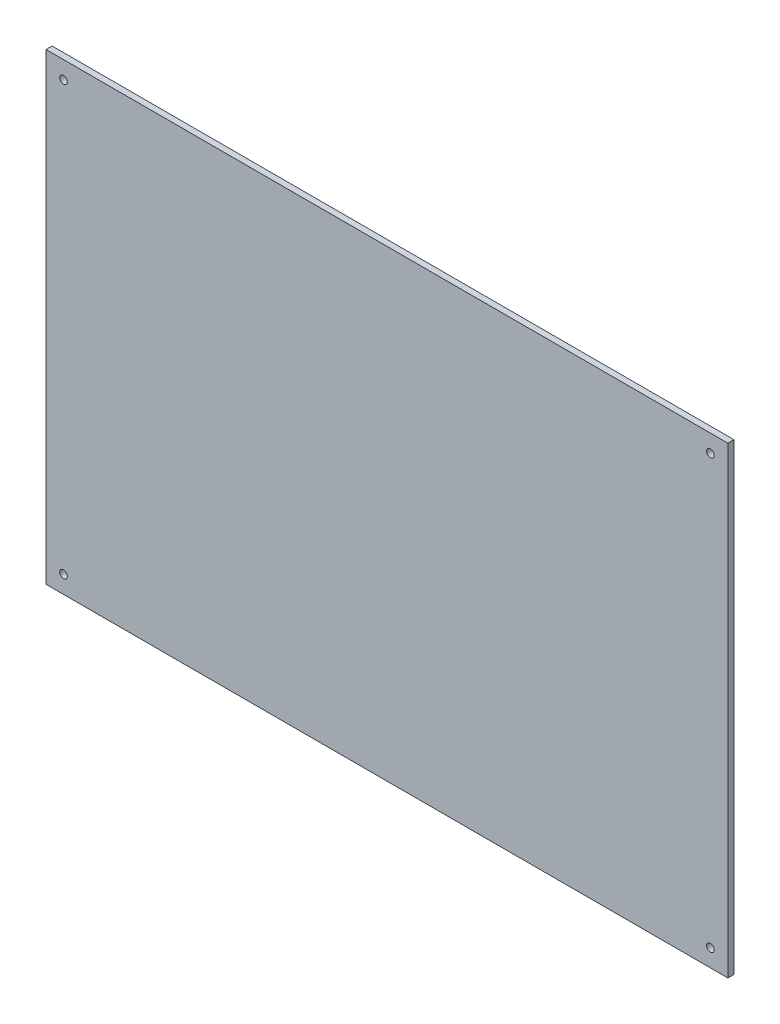
SolidWorks part; units mm, degrees
ref_plane "Piano frontale" through (0, 0, 0) normal (0, 0, 1) x (1, 0, 0)
ref_plane "Piano superiore" through (0, 0, 0) normal (0, 1, 0) x (1, 0, 0)
ref_plane "Piano destro" through (0, 0, 0) normal (1, 0, 0) x (0, 0, -1)
sketch "Schizzo1" plane through (0, 0, 0) normal (0, 0, 1) x (1, 0, 0)
  line L0 (-224.5, 305) -> (-224.5, 0) construction
  line L1 (0, 0) -> (-449, 0)
  line L2 (0, 0) -> (0, 305)
  line L3 (0, 305) -> (-449, 305)
  line L4 (-449, 0) -> (-449, 305)
  line L7 (-449, 152.5) -> (0, 152.5) construction
  circle A0 centre (-437.5, 293.5) radius 2.5
  circle A1 centre (-11.5, 293.5) radius 2.5
  circle A2 centre (-437.5, 11.5) radius 2.5
  circle A3 centre (-11.5, 11.5) radius 2.5
  dimension "D3" = 11.5
  dimension "D4" = 5
  dimension "D1" = 449
  dimension "D2" = 11.5
  dimension "314" = 305
extrude "Estrusione-Estrusione1" add sketch "Schizzo1" along normal blind 4
